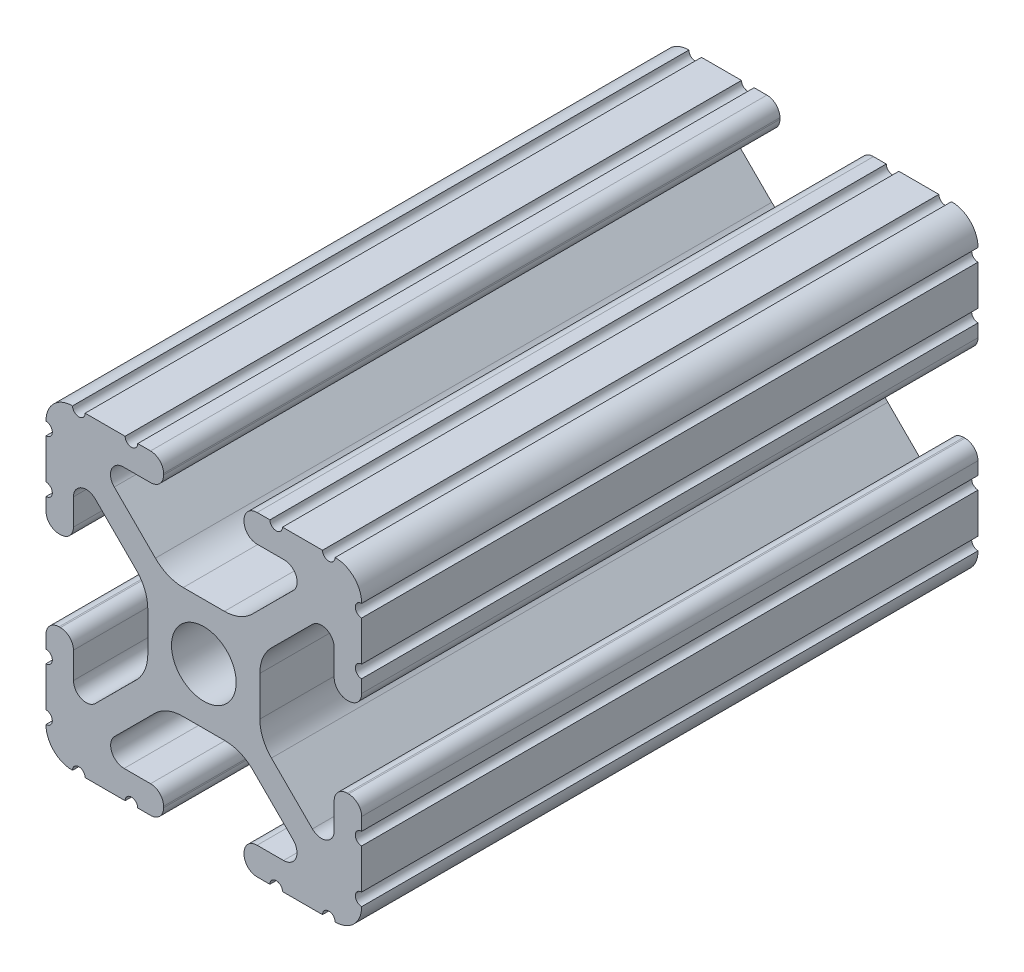
SolidWorks part; units mm, degrees
ref_plane "Front Plane" through (0, 0, 0) normal (0, 0, 1) x (1, 0, 0)
ref_plane "Top Plane" through (0, 0, 0) normal (0, 1, 0) x (1, 0, 0)
ref_plane "Right Plane" through (0, 0, 0) normal (1, 0, 0) x (0, 0, -1)
sketch "Sketch1" plane through (0, 0, 0) normal (0, 0, 1) x (1, 0, 0)
  line L88 (-7.1797, -8.6452) -> (-3.9523, -5.4237)
  line L89 (-1.7093, -4.4958) -> (1.7093, -4.4958)
  line L90 (3.9523, -5.4237) -> (7.1797, -8.6452)
  line L91 (6.4164, -10.4902) -> (4.2875, -10.4902)
  line L92 (3.2385, -11.5392) -> (3.2385, -11.651)
  line L93 (4.2875, -12.7) -> (5.3171, -12.7)
  line L94 (6.3331, -12.7) -> (9.5504, -12.7)
  line L95 (12.7, -9.5504) -> (12.7, -6.3331)
  line L96 (12.7, -5.3171) -> (12.7, -4.2875)
  line L97 (11.651, -3.2385) -> (11.5392, -3.2385)
  line L98 (10.4902, -4.2875) -> (10.4902, -6.4021)
  line L99 (8.7371, -7.1294) -> (5.441, -3.8408)
  line L100 (4.5085, -1.5932) -> (4.5085, 1.5932)
  line L101 (5.441, 3.8408) -> (8.7371, 7.1294)
  line L102 (10.4902, 6.4021) -> (10.4902, 4.2875)
  line L103 (11.5392, 3.2385) -> (11.651, 3.2385)
  line L104 (12.7, 4.2875) -> (12.7, 5.3171)
  line L105 (12.7, 6.3331) -> (12.7, 9.5504)
  line L106 (9.5504, 12.7) -> (6.3331, 12.7)
  line L107 (5.3171, 12.7) -> (4.2875, 12.7)
  line L108 (3.2385, 11.651) -> (3.2385, 11.5392)
  line L109 (4.2875, 10.4902) -> (6.4768, 10.4902)
  line L110 (7.207, 8.7244) -> (3.8983, 5.4232)
  line L111 (1.6558, 4.4958) -> (-1.6558, 4.4958)
  line L112 (-3.8983, 5.4232) -> (-7.207, 8.7244)
  line L113 (-6.4768, 10.4902) -> (-4.2875, 10.4902)
  line L114 (-3.2385, 11.5392) -> (-3.2385, 11.651)
  line L115 (-4.2875, 12.7) -> (-5.3171, 12.7)
  line L116 (-6.3331, 12.7) -> (-9.5504, 12.7)
  line L117 (-12.7, 9.5504) -> (-12.7, 6.3331)
  line L118 (-12.7, 5.3171) -> (-12.7, 4.2875)
  line L119 (-11.651, 3.2385) -> (-11.5392, 3.2385)
  line L120 (-10.4902, 4.2875) -> (-10.4902, 6.4021)
  line L121 (-8.7371, 7.1294) -> (-5.441, 3.8408)
  line L122 (-4.5085, 1.5932) -> (-4.5085, -1.5932)
  line L123 (-5.441, -3.8408) -> (-8.7371, -7.1294)
  line L124 (-10.4902, -6.4021) -> (-10.4902, -4.2875)
  line L125 (-11.5392, -3.2385) -> (-11.651, -3.2385)
  line L126 (-12.7, -4.2875) -> (-12.7, -5.3171)
  line L127 (-12.7, -6.3331) -> (-12.7, -9.5504)
  line L128 (-9.5504, -12.7) -> (-6.3331, -12.7)
  line L129 (-5.3171, -12.7) -> (-4.2875, -12.7)
  line L130 (-3.2385, -11.651) -> (-3.2385, -11.5392)
  line L131 (-4.2875, -10.4902) -> (-6.4164, -10.4902)
  circle A1 centre (0, 0) radius 2.6035
  arc A104 (-7.1797, -8.6452) -> (-6.4164, -10.4902) centre (-6.4164, -9.4098) ccw
  arc A105 (-1.7093, -4.4958) -> (-3.9523, -5.4237) centre (-1.7093, -7.6708) ccw
  arc A106 (3.9523, -5.4237) -> (1.7093, -4.4958) centre (1.7093, -7.6708) ccw
  arc A107 (6.4164, -10.4902) -> (7.1797, -8.6452) centre (6.4164, -9.4098) ccw
  arc A108 (4.2875, -10.4902) -> (3.2385, -11.5392) centre (4.2875, -11.5392) ccw
  arc A109 (3.2385, -11.651) -> (4.2875, -12.7) centre (4.2875, -11.651) ccw
  arc A110 (6.3331, -12.7) -> (5.3171, -12.7) centre (5.8251, -12.7) ccw
  arc A111 (10.5664, -12.6998) -> (9.5504, -12.7) centre (10.0584, -12.7) ccw
  arc A112 (10.5664, -12.6998) -> (12.6998, -10.5664) centre (10.5918, -10.5918) ccw
  arc A113 (12.7, -9.5504) -> (12.6998, -10.5664) centre (12.7, -10.0584) ccw
  arc A114 (12.7, -5.3171) -> (12.7, -6.3331) centre (12.7, -5.8251) ccw
  arc A115 (12.7, -4.2875) -> (11.651, -3.2385) centre (11.651, -4.2875) ccw
  arc A116 (11.5392, -3.2385) -> (10.4902, -4.2875) centre (11.5392, -4.2875) ccw
  arc A117 (8.7371, -7.1294) -> (10.4902, -6.4021) centre (9.4628, -6.4021) ccw
  arc A118 (4.5085, -1.5932) -> (5.441, -3.8408) centre (7.6835, -1.5932) ccw
  arc A119 (5.441, 3.8408) -> (4.5085, 1.5932) centre (7.6835, 1.5932) ccw
  arc A120 (10.4902, 6.4021) -> (8.7371, 7.1294) centre (9.4628, 6.4021) ccw
  arc A121 (10.4902, 4.2875) -> (11.5392, 3.2385) centre (11.5392, 4.2875) ccw
  arc A122 (11.651, 3.2385) -> (12.7, 4.2875) centre (11.651, 4.2875) ccw
  arc A123 (12.7, 6.3331) -> (12.7, 5.3171) centre (12.7, 5.8251) ccw
  arc A124 (12.6998, 10.5664) -> (12.7, 9.5504) centre (12.7, 10.0584) ccw
  arc A125 (12.6998, 10.5664) -> (10.5664, 12.6998) centre (10.5918, 10.5918) ccw
  arc A126 (9.5504, 12.7) -> (10.5664, 12.6998) centre (10.0584, 12.7) ccw
  arc A127 (5.3171, 12.7) -> (6.3331, 12.7) centre (5.8251, 12.7) ccw
  arc A128 (4.2875, 12.7) -> (3.2385, 11.651) centre (4.2875, 11.651) ccw
  arc A129 (3.2385, 11.5392) -> (4.2875, 10.4902) centre (4.2875, 11.5392) ccw
  arc A130 (7.207, 8.7244) -> (6.4768, 10.4902) centre (6.4768, 9.4563) ccw
  arc A131 (1.6558, 4.4958) -> (3.8983, 5.4232) centre (1.6558, 7.6708) ccw
  arc A132 (-3.8983, 5.4232) -> (-1.6558, 4.4958) centre (-1.6558, 7.6708) ccw
  arc A133 (-6.4768, 10.4902) -> (-7.207, 8.7244) centre (-6.4768, 9.4563) ccw
  arc A134 (-4.2875, 10.4902) -> (-3.2385, 11.5392) centre (-4.2875, 11.5392) ccw
  arc A135 (-3.2385, 11.651) -> (-4.2875, 12.7) centre (-4.2875, 11.651) ccw
  arc A136 (-6.3331, 12.7) -> (-5.3171, 12.7) centre (-5.8251, 12.7) ccw
  arc A137 (-10.5664, 12.6998) -> (-9.5504, 12.7) centre (-10.0584, 12.7) ccw
  arc A138 (-10.5664, 12.6998) -> (-12.6998, 10.5664) centre (-10.5918, 10.5918) ccw
  arc A139 (-12.7, 9.5504) -> (-12.6998, 10.5664) centre (-12.7, 10.0584) ccw
  arc A140 (-12.7, 5.3171) -> (-12.7, 6.3331) centre (-12.7, 5.8251) ccw
  arc A141 (-12.7, 4.2875) -> (-11.651, 3.2385) centre (-11.651, 4.2875) ccw
  arc A142 (-11.5392, 3.2385) -> (-10.4902, 4.2875) centre (-11.5392, 4.2875) ccw
  arc A143 (-8.7371, 7.1294) -> (-10.4902, 6.4021) centre (-9.4628, 6.4021) ccw
  arc A144 (-4.5085, 1.5932) -> (-5.441, 3.8408) centre (-7.6835, 1.5932) ccw
  arc A145 (-5.441, -3.8408) -> (-4.5085, -1.5932) centre (-7.6835, -1.5932) ccw
  arc A146 (-10.4902, -6.4021) -> (-8.7371, -7.1294) centre (-9.4628, -6.4021) ccw
  arc A147 (-10.4902, -4.2875) -> (-11.5392, -3.2385) centre (-11.5392, -4.2875) ccw
  arc A148 (-11.651, -3.2385) -> (-12.7, -4.2875) centre (-11.651, -4.2875) ccw
  arc A149 (-12.7, -6.3331) -> (-12.7, -5.3171) centre (-12.7, -5.8251) ccw
  arc A150 (-12.6998, -10.5664) -> (-12.7, -9.5504) centre (-12.7, -10.0584) ccw
  arc A151 (-12.6998, -10.5664) -> (-10.5664, -12.6998) centre (-10.5918, -10.5918) ccw
  arc A152 (-9.5504, -12.7) -> (-10.5664, -12.6998) centre (-10.0584, -12.7) ccw
  arc A153 (-5.3171, -12.7) -> (-6.3331, -12.7) centre (-5.8251, -12.7) ccw
  arc A154 (-4.2875, -12.7) -> (-3.2385, -11.651) centre (-4.2875, -11.651) ccw
  arc A155 (-3.2385, -11.5392) -> (-4.2875, -10.4902) centre (-4.2875, -11.5392) ccw
extrude "Boss-Extrude1" add sketch "Sketch1" along normal mid plane 49.6
